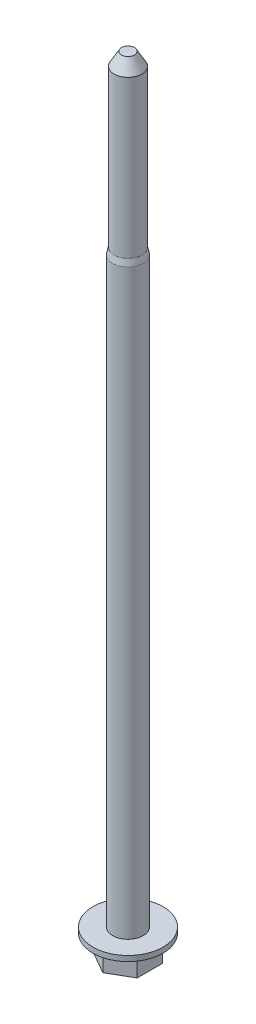
SolidWorks part; units mm, degrees
ref_plane "Front Plane" through (0, 0, 0) normal (0, 0, 1) x (1, 0, 0)
ref_plane "Top Plane" through (0, 0, 0) normal (0, 1, 0) x (1, 0, 0)
ref_plane "Right Plane" through (0, 0, 0) normal (1, 0, 0) x (0, 0, -1)
sketch "Sketch1" plane through (0, 0, 0) normal (0, 1, 0) x (1, 0, 0)
  line L1 (0, -3.9375) -> (3.41, -1.9688)
  line L2 (3.41, -1.9688) -> (3.41, 1.9688)
  line L3 (3.41, 1.9688) -> (0, 3.9375)
  line L4 (0, 3.9375) -> (-3.41, 1.9688)
  line L5 (-3.41, 1.9688) -> (-3.41, -1.9688)
  line L6 (-3.41, -1.9688) -> (0, -3.9375)
  circle A0 centre (0, 0) radius 3.41 construction
  dimension "D1" = 6.82
extrude "Boss-Extrude1" add sketch "Sketch1" along normal blind 3.4
sketch "Sketch2" plane through (0, 3.4, 0) normal (0, 1, 0) x (1, 0, 0)
  circle A0 centre (0, 0) radius 5.48
  dimension "D1" = 10.96
extrude "Boss-Extrude2" add sketch "Sketch2" along normal blind 0.83
sketch "Sketch3" plane through (0, 4.23, 0) normal (0, 1, 0) x (1, 0, 0)
  circle A0 centre (0, 0) radius 2.385
  dimension "D1" = 4.77
extrude "Boss-Extrude3" add sketch "Sketch3" along normal blind 92
sketch "Sketch4" plane through (0, 96.23, 0) normal (0, 1, 0) x (1, 0, 0)
  circle A0 centre (0, 0) radius 2.165
  dimension "D1" = 4.33
extrude "Boss-Extrude4" add sketch "Sketch4" along normal blind 26.5
chamfer "Chamfer1" distance 2 angle 30 1 edges at (0, 122.73, 2.165)
chamfer "Chamfer2" distance 1 angle 12 1 edges at (0, 96.23, 2.385)
